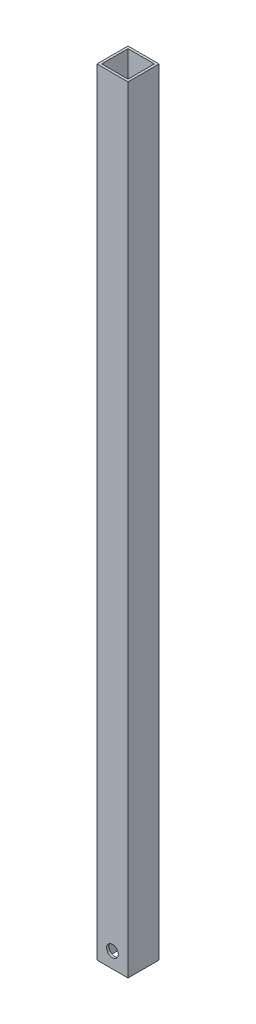
SolidWorks part; units mm, degrees
ref_plane "Alzado" through (0, 0, 0) normal (0, 0, 1) x (1, 0, 0)
ref_plane "Planta" through (0, 0, 0) normal (0, 1, 0) x (1, 0, 0)
ref_plane "Vista lateral" through (0, 0, 0) normal (1, 0, 0) x (0, 0, -1)
sketch "Croquis1" plane through (0, 0, 0) normal (0, 1, 0) x (1, 0, 0)
  line L0 (-17, 17) -> (17, 17)
  line L1 (-20, 20) -> (20, 20)
  line L2 (-20, 20) -> (-20, -20)
  line L3 (-20, -20) -> (20, -20)
  line L4 (20, 20) -> (20, -20)
  line L5 (-20, 20) -> (20, -20) construction
  line L6 (-20, -20) -> (20, 20) construction
  line L7 (17, 17) -> (17, -17)
  line L8 (-17, -17) -> (17, -17)
  line L9 (-17, 17) -> (-17, -17)
  point P0 (0, 0)
  dimension "D1" = 3
extrude "Saliente-Extruir1" add sketch "Croquis1" along normal blind 1000
sketch "Croquis2" plane through (0, 0, -20) normal (0, 0, -1) x (-1, 0, 0)
  line L0 (0, 0) -> (0, 20)
  circle A0 centre (0, 20) radius 7.5
  dimension "D1" = 15
extrude "Cortar-Extruir1" cut sketch "Croquis2" along direction (0, 0, -1) on the side against the normal through all contours A0
